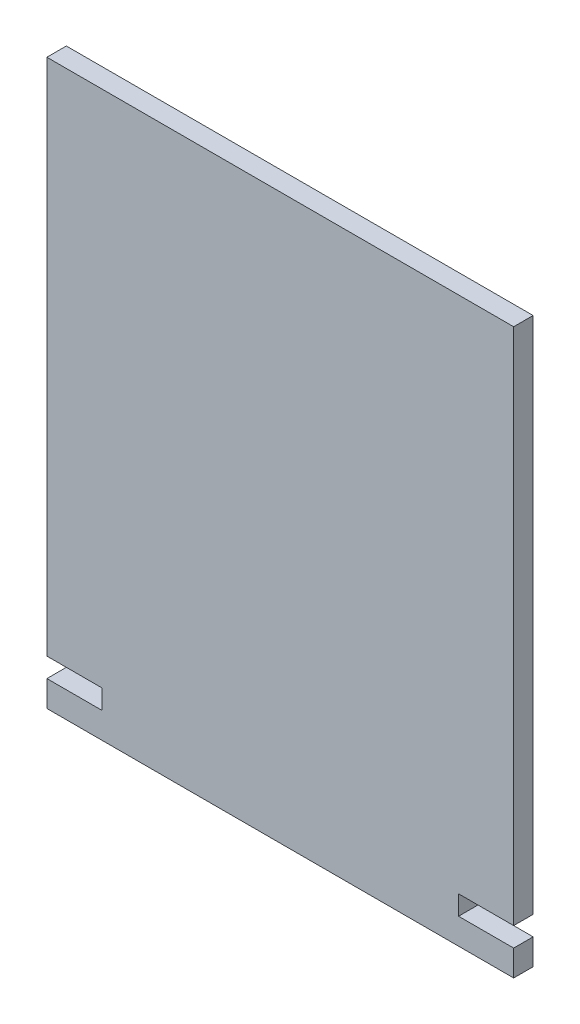
SolidWorks part; units mm, degrees
ref_plane "前视基准面" through (0, 0, 0) normal (0, 0, 1) x (1, 0, 0)
ref_plane "上视基准面" through (0, 0, 0) normal (0, 1, 0) x (1, 0, 0)
ref_plane "右视基准面" through (0, 0, 0) normal (1, 0, 0) x (0, 0, -1)
sketch "草图1" plane through (0, 0, 0) normal (0, 0, 1) x (1, 0, 0)
  line L0 (0, 48.6887) -> (0, -34.7075) construction
  line L1 (36, -21.5283) -> (-36, -21.5283)
  line L2 (-36, -21.5283) -> (-36, -17.5283)
  line L3 (-36, -17.5283) -> (-27.5, -17.5283)
  line L4 (-27.5, -17.5283) -> (-27.5, -14.5283)
  line L5 (-27.5, -14.5283) -> (-36, -14.5283)
  line L6 (-36, -14.5283) -> (-36, 65.4717)
  line L7 (-36, 65.4717) -> (36, 65.4717)
  line L8 (36, -21.5283) -> (36, -17.5283)
  line L9 (36, -17.5283) -> (27.5, -17.5283)
  line L10 (27.5, -17.5283) -> (27.5, -14.5283)
  line L11 (27.5, -14.5283) -> (36, -14.5283)
  line L12 (36, -14.5283) -> (36, 65.4717)
  point P11 (31.75, -17.5283)
  point P12 (0, -21.5283)
  point P17 (0, 65.4717)
  dimension "D1" = 72
  dimension "D2" = 3
  dimension "D3" = 8.5
  dimension "D4" = 72
  dimension "D5" = 80
  dimension "D6" = 4
extrude "凸台-拉伸1" add sketch "草图1" along normal blind 3
